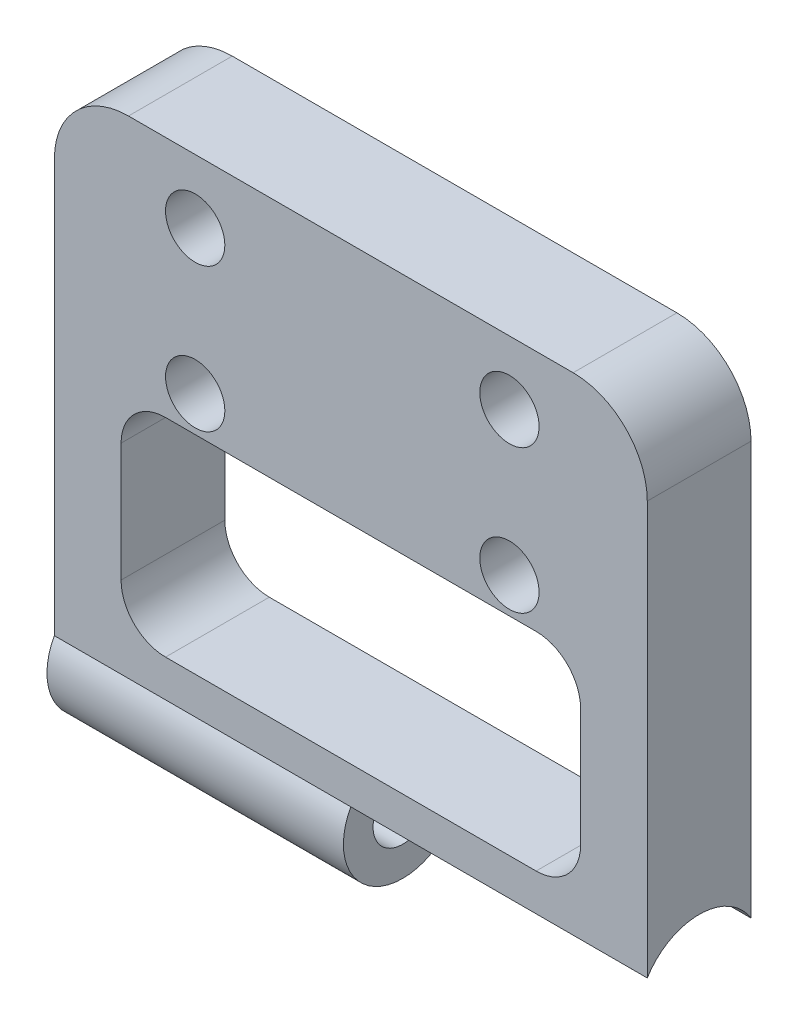
SolidWorks part; units mm, degrees
ref_plane "Front Plane" through (0, 0, 0) normal (0, 0, 1) x (1, 0, 0)
ref_plane "Top Plane" through (0, 0, 0) normal (0, 1, 0) x (1, 0, 0)
ref_plane "Right Plane" through (0, 0, 0) normal (1, 0, 0) x (0, 0, -1)
sketch "Sketch1" plane through (0, 0, 0) normal (0, 0, 1) x (1, 0, 0)
  line L1 (-22.2292, 16.4644) -> (17.7708, 16.4644)
  line L2 (-22.2292, 16.4644) -> (-22.2292, -18.5356)
  line L3 (-22.2292, -18.5356) -> (17.7708, -18.5356)
  line L4 (17.7708, 16.4644) -> (17.7708, -18.5356)
  dimension "D1" = 40
  dimension "D2" = 35
extrude "Boss-Extrude1" add sketch "Sketch1" along normal blind 7
sketch "Sketch2" plane through (17.7708, 0, 0) normal (1, 0, 0) x (0, 0, -1)
  line L0 (-7, -18.5356) -> (0, -18.5356) construction
  circle A0 centre (-3.5, -18.5356) radius 4.1
  dimension "D1" = 8.2
extrude "Cut-Extrude1" cut sketch "Sketch2" against normal blind 20
ref_plane "Plane1" through (-13.2292, 0, 0) normal (1, 0, 0) x (0, 0, -1)
sketch "Sketch3" plane through (-13.2292, 0, 0) normal (1, 0, 0) x (0, 0, -1)
  circle A0 centre (-3.5, -18.3367) radius 4
  circle A1 centre (-3.5, -18.3367) radius 2
  dimension "D1" = 8
  dimension "D2" = 4
extrude "Boss-Extrude2" add sketch "Sketch3" against normal blind 9 and the other way blind 11
fillet "Fillet1" radius 5 2 edges at (-22.2292, 16.4644, 3.5) (17.7708, 16.4644, 3.5)
sketch "Sketch4" plane through (0, 0, 0) normal (0, 0, -1) x (-1, 0, 0)
  line L1 (17.7292, 0.0998) -> (-13.2708, 0.0998)
  line L2 (17.7292, 0.0998) -> (17.7292, -13.9002)
  line L3 (17.7292, -13.9002) -> (-13.2708, -13.9002)
  line L4 (-13.2708, 0.0998) -> (-13.2708, -13.9002)
  line L5 (22.2292, 11.4644) -> (22.2292, -16.4002) construction
  line L6 (22.2292, -16.4002) -> (2.2292, -16.4002) construction
  circle A0 centre (-8.4708, 12.1644) radius 2
  circle A1 centre (12.7292, 12.1644) radius 2
  circle A2 centre (12.7292, 2.4894) radius 2
  circle A3 centre (-8.4708, 2.4894) radius 2
  dimension "D1" = 4
  dimension "D2" = 4
  dimension "D3" = 4
  dimension "D4" = 4
  dimension "D5" = 31
  dimension "D6" = 4.5
  dimension "D7" = 2.5
  dimension "D8" = 14
extrude "Cut-Extrude2" cut sketch "Sketch4" against normal through all
fillet "Fillet2" radius 3 4 edges at (13.2708, 0.0998, 3.5) (13.2708, -13.9002, 3.5) (-17.7292, -13.9002, 3.5) (-17.7292, 0.0998, 3.5)
sketch "Sketch5" plane through (-22.2292, 0, 0) normal (-1, 0, 0) x (0, 0, 1)
  circle A0 centre (3.5, -18.3367) radius 2
  arc A1 (1.5099, -18.5356) -> (5.4901, -18.5356) centre (3.5, -18.3367) ccw construction
extrude "Cut-Extrude3" cut sketch "Sketch5" against normal through all
